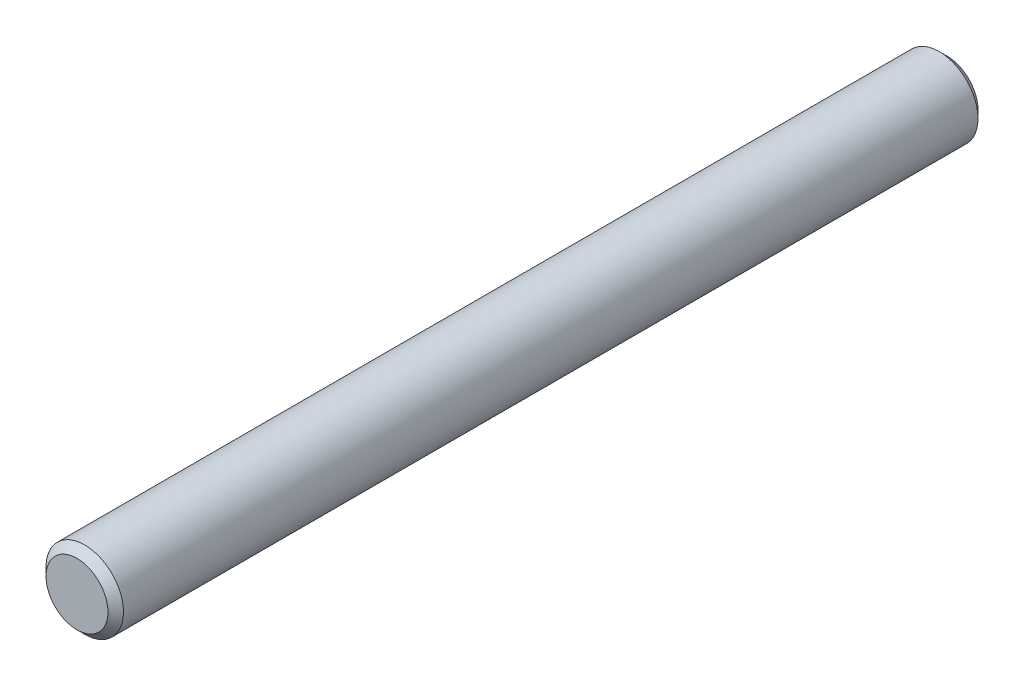
SolidWorks part; units mm, degrees
material "Plain Carbon Steel"
ref_plane "Front" through (0, 0, 0) normal (0, 0, 1) x (1, 0, 0)
ref_plane "Top" through (0, 0, 0) normal (0, 1, 0) x (1, 0, 0)
ref_plane "Right" through (0, 0, 0) normal (1, 0, 0) x (0, 0, -1)
sketch "Sketch1" plane through (0, 0, 0) normal (0, 0, 1) x (1, 0, 0)
  circle A0 centre (0, 0) radius 4.7625
  dimension "dia" = 9.525
extrude "Extrude1" add sketch "Sketch1" along normal mid plane 106.9975
sketch "Sketch2" plane through (0, 0, 0) normal (1, 0, 0) x (0, 0, -1)
  line L0 (53.4988, 4.7625) -> (50.9588, 4.7625) construction
  line L1 (53.4988, 4.7625) -> (-53.4988, 4.7625) construction
  line L2 (50.9588, 4.7625) -> (46.1962, 4.7625) construction
  line L3 (46.1962, 4.7625) -> (34.7663, 4.7625) construction
  line L4 (34.7663, 4.7625) -> (30.0038, 4.7625) construction
  line L8 (40.4813, 4.7625) -> (40.4813, -4.7625) construction
  line L9 (-53.4988, -4.7625) -> (53.4988, -4.7625) construction
  line L10 (30.0038, 4.7625) -> (18.5738, 4.7625) construction
  line L11 (18.5738, 4.7625) -> (13.8113, 4.7625) construction
  line L12 (13.8113, 4.7625) -> (2.3813, 4.7625) construction
  line L13 (2.3813, 4.7625) -> (-2.3812, 4.7625) construction
  line L14 (-2.3812, 4.7625) -> (-13.8112, 4.7625) construction
  line L15 (27.4638, 4.7625) -> (27.4638, -4.7625) construction
  line L16 (11.2713, 4.7625) -> (11.2713, -4.7625) construction
  line L17 (-4.9212, 4.7625) -> (-4.9212, -4.7625) construction
  line L18 (-13.8112, 4.7625) -> (-18.5737, 4.7625) construction
  line L19 (38.0175, 4.7625) -> (42.9451, 4.7625) construction
  line L20 (38.0175, 4.7625) -> (38.0175, -4.7625) construction
  line L21 (38.0175, -4.7625) -> (42.9451, -4.7625) construction
  line L22 (42.9451, 4.7625) -> (42.9451, -4.7625) construction
  line L23 (-18.5737, 4.7625) -> (-30.0037, 4.7625) construction
  line L24 (-30.0037, 4.7625) -> (-34.7662, 4.7625) construction
  line L25 (-34.7662, 4.7625) -> (-46.1962, 4.7625) construction
  line L26 (-46.1962, 4.7625) -> (-50.9587, 4.7625) construction
  line L27 (-21.1137, 4.7625) -> (-21.1137, -4.7625) construction
  line L28 (-37.3062, 4.7625) -> (-37.3062, -4.7625) construction
  point P0 (-53.4988, 4.7625)
  point P1 (53.4988, 4.7625)
  point P30 (40.4813, 4.7625)
  dimension "D1" = 2.54
  dimension "D2" = 4.7625
  dimension "D3" = 11.43
  dimension "D4" = 4.7625
  dimension "D5" = 11.43
  dimension "D6" = 4.7625
  dimension "D7" = 11.43
  dimension "D8" = 4.7625
  dimension "D9" = 11.43
  dimension "D10" = 4.9276
  dimension "D11" = 2.54
  dimension "D12" = 2.54
  dimension "D13" = 2.54
  dimension "D14" = 4.7625
  dimension "D15" = 4.7625
  dimension "D16" = 11.43
  dimension "D17" = 11.43
  dimension "D18" = 4.7625
  dimension "D19" = 2.54
  dimension "D20" = 2.54
chamfer "Chamfer1" distance 0.9525 angle 45 2 edges at (4.7625, 0, -53.4988) (4.7625, 0, 53.4988)
equation "\"D1@Chamfer1\" = \"dia@Sketch1\" * .1"
